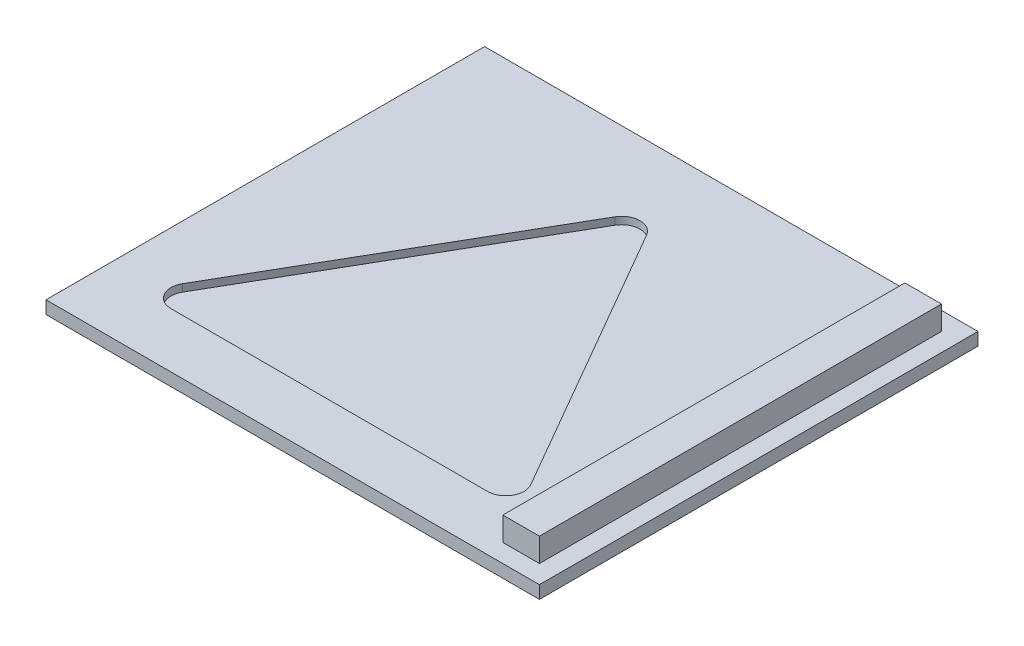
SolidWorks part; units mm, degrees
ref_plane "Front Plane" through (0, 0, 0) normal (0, 0, 1) x (1, 0, 0)
ref_plane "Top Plane" through (0, 0, 0) normal (0, 1, 0) x (1, 0, 0)
ref_plane "Right Plane" through (0, 0, 0) normal (1, 0, 0) x (0, 0, -1)
sketch "Sketch1" plane through (0, 0, 0) normal (0, 1, 0) x (1, 0, 0)
  line L0 (0, 0) -> (1, 0) construction
  line L5 (13, -12) -> (-13, -12)
  line L6 (13, -12) -> (13, 12)
  line L7 (13, 12) -> (-13, 12)
  line L8 (-13, -12) -> (-13, 12)
  line L9 (13, -12) -> (-13, 12) construction
  line L10 (13, 12) -> (-13, -12) construction
  line L12 (12, -11) -> (-10, -11) construction
  line L13 (12, -11) -> (12, 11) construction
  line L14 (12, 11) -> (-10, 11) construction
  line L15 (-10, -11) -> (-10, 11) construction
  line L16 (12, -11) -> (-10, 11) construction
  line L17 (12, 11) -> (-10, -11) construction
  point P0 (0, 0)
  dimension "D1" = 22
  dimension "D2" = 1
  dimension "D3" = 1
  dimension "D4" = 3
extrude "Boss-Extrude1" add sketch "Sketch1" along normal blind 0.7
sketch "Sketch2" plane through (0, 0.7, 0) normal (0, 1, 0) x (1, 0, 0)
  line L0 (0, 0) -> (11, 0) construction
  line L2 (12, -11) -> (10, -11)
  line L3 (12, -11) -> (12, 11)
  line L4 (12, 11) -> (10, 11)
  line L5 (10, -11) -> (10, 11)
  line L6 (12, -11) -> (10, 11) construction
  line L7 (12, 11) -> (10, -11) construction
  line L8 (13, 12) -> (-13, 12) construction
  line L9 (13, -12) -> (13, 12) construction
  dimension "D1" = 1
  dimension "D2" = 2
  dimension "D3" = 1
extrude "Boss-Extrude2" add sketch "Sketch2" along normal blind 1.3
sketch "Sketch3" plane through (0, 0.7, 0) normal (0, 1, 0) x (1, 0, 0)
  line L0 (-2.366, 7.5) -> (-11.0263, -7.5)
  line L1 (-10.1603, -9) -> (7.1603, -9)
  line L2 (8.0263, -7.5) -> (-0.634, 7.5)
  line L3 (-1.5, 9) -> (-1.5, 12) construction
  line L4 (13, 12) -> (-13, 12) construction
  line L5 (-1.5, -9) -> (-1.5, -12) construction
  line L6 (-13, -12) -> (13, -12) construction
  line L7 (-13, -9) -> (-11.8923, -9) construction
  line L9 (8.8923, -9) -> (10, -9) construction
  line L14 (-13, 12) -> (-13, -12) construction
  line L15 (10, 11) -> (10, -11) construction
  arc A0 (8.0263, -7.5) -> (7.1603, -9) centre (7.1603, -8) cw
  arc A1 (-10.1603, -9) -> (-11.0263, -7.5) centre (-10.1603, -8) cw
  arc A2 (-0.634, 7.5) -> (-2.366, 7.5) centre (-1.5, 7) ccw
  point P2 (0, 0.999)
  dimension "D1" = 1
  dimension "D3" = 3
extrude "Cut-Extrude2" cut sketch "Sketch3" against normal blind 0.4 contours A2 L0 A1 L1 A0 L2
sketch "Sketch4" plane through (0, 0.7, 0) normal (0, 1, 0) x (1, 0, 0)
  line L0 (-13, -12) -> (13, -12) construction
  line L1 (-13, 12) -> (-14, 12)
  line L2 (-13, 12) -> (-13, -12)
  line L3 (-13, -12) -> (-14, -12)
  line L4 (-14, 12) -> (-14, -12)
  dimension "D1" = 1
extrude "Boss-Extrude3" add sketch "Sketch4" against normal up to surface (0.7 mm away) up to face at (0, 0, 0)
